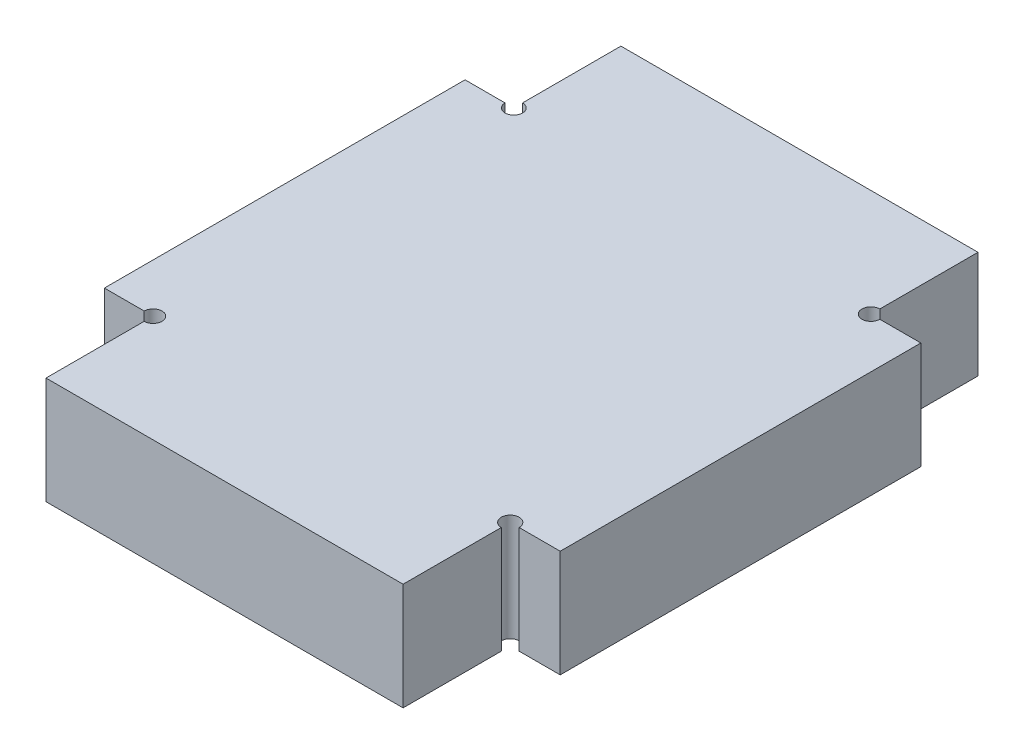
SolidWorks part; units mm, degrees
ref_plane "Front Plane" through (0, 0, 0) normal (0, 0, 1) x (1, 0, 0)
ref_plane "Top Plane" through (0, 0, 0) normal (0, 1, 0) x (1, 0, 0)
ref_plane "Right Plane" through (0, 0, 0) normal (1, 0, 0) x (0, 0, -1)
sketch "Sketch1" plane through (0, 0, 0) normal (0, 1, 0) x (1, 0, 0)
  line L0 (0.25, 5.3321) -> (1.4, 5.3321)
  line L1 (1.4, 5.3321) -> (1.4, -4.7679)
  line L2 (1.4, -4.7679) -> (0.25, -4.7679)
  line L3 (0, -5.0179) -> (0, -7.7679)
  line L4 (0, -7.7679) -> (-10, -7.7679)
  line L5 (0, 5.5821) -> (0, 8.3321)
  line L6 (0, 8.3321) -> (-10, 8.3321)
  line L7 (-10, 8.3321) -> (-10, 5.5774)
  line L8 (-10.2453, 5.3321) -> (-11.3647, 5.3321)
  line L9 (-10, -7.7679) -> (-10, -5.0179)
  line L10 (-10.25, -4.7679) -> (-11.3647, -4.7679)
  line L11 (-11.3647, -4.7679) -> (-11.3647, 5.3321)
  arc A0 (-10.2453, 5.3321) -> (-10, 5.5774) centre (-10, 5.3321) ccw
  arc A1 (-10, -5.0179) -> (-10.25, -4.7679) centre (-10, -4.7679) ccw
  arc A2 (0.25, -4.7679) -> (0, -5.0179) centre (0, -4.7679) ccw
  arc A3 (0, 5.5821) -> (0.25, 5.3321) centre (0, 5.3321) ccw
  dimension "D8" = 10
  dimension "D1" = 10.1
  dimension "D2" = 1.4
  dimension "D3" = 3
  dimension "D4" = 3
  dimension "D5" = 10
  dimension "D6" = 10
  dimension "D9" = 10
extrude "Boss-Extrude1" add sketch "Sketch1" along normal blind 3
